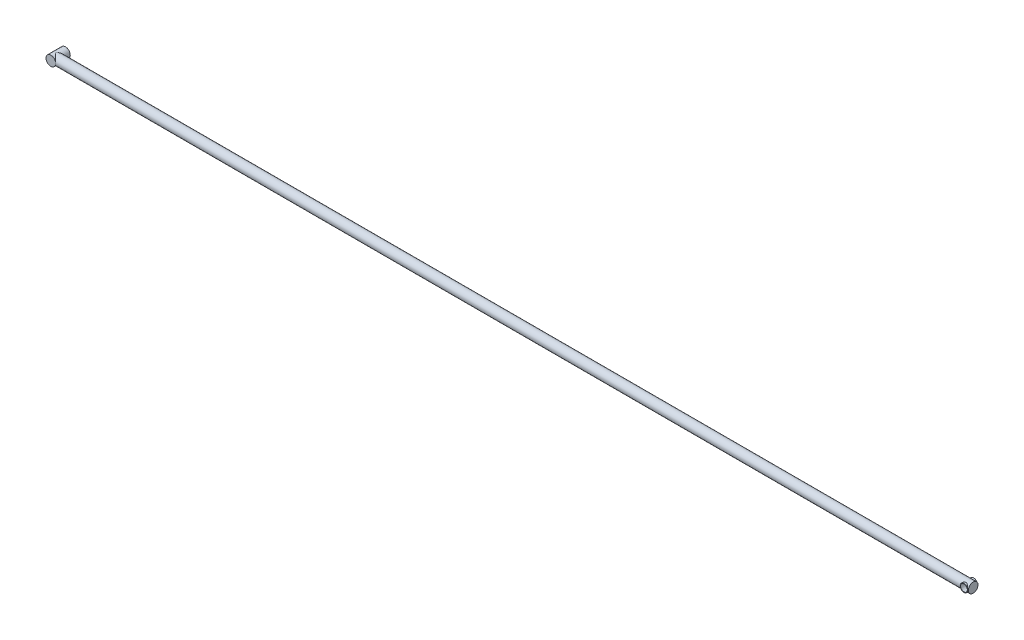
SolidWorks part; units mm, degrees
material "普通碳钢"
ref_plane "前视基准面" through (0, 0, 0) normal (0, 0, 1) x (1, 0, 0)
ref_plane "上视基准面" through (0, 0, 0) normal (0, 1, 0) x (1, 0, 0)
ref_plane "右视基准面" through (0, 0, 0) normal (1, 0, 0) x (0, 0, -1)
sketch "草图1" plane through (0, 0, 0) normal (0, 0, 1) x (1, 0, 0)
  circle A0 centre (0, 0) radius 1
  dimension "D1" = 2
extrude "凸台-拉伸1" add sketch "草图1" against normal blind 3
sketch "草图2" plane through (0, 0, 0) normal (1, 0, 0) x (0, 0, -1)
  line L0 (3, 0) -> (0, 0) construction
  circle A0 centre (1, 0) radius 1
  dimension "D1" = 2
extrude "凸台-拉伸2" add sketch "草图2" along normal blind 189
sketch "草图3" plane through (0, 0, 0) normal (0, 0, 1) x (1, 0, 0)
  line L1 (189, -1) -> (189, 1) construction
  circle A0 centre (188.1, 0) radius 0.8
  dimension "D1" = 1.6
  dimension "D2" = 0.9
extrude "凸台-拉伸3" add sketch "草图3" against normal blind 2
sketch "草图4" plane through (0, 0, 0) normal (0, 0, 1) x (1, 0, 0)
  circle A0 centre (188.1, 0) radius 0.7
  dimension "D1" = 1.4
extrude "切除-拉伸1" cut sketch "草图4" against normal through all
